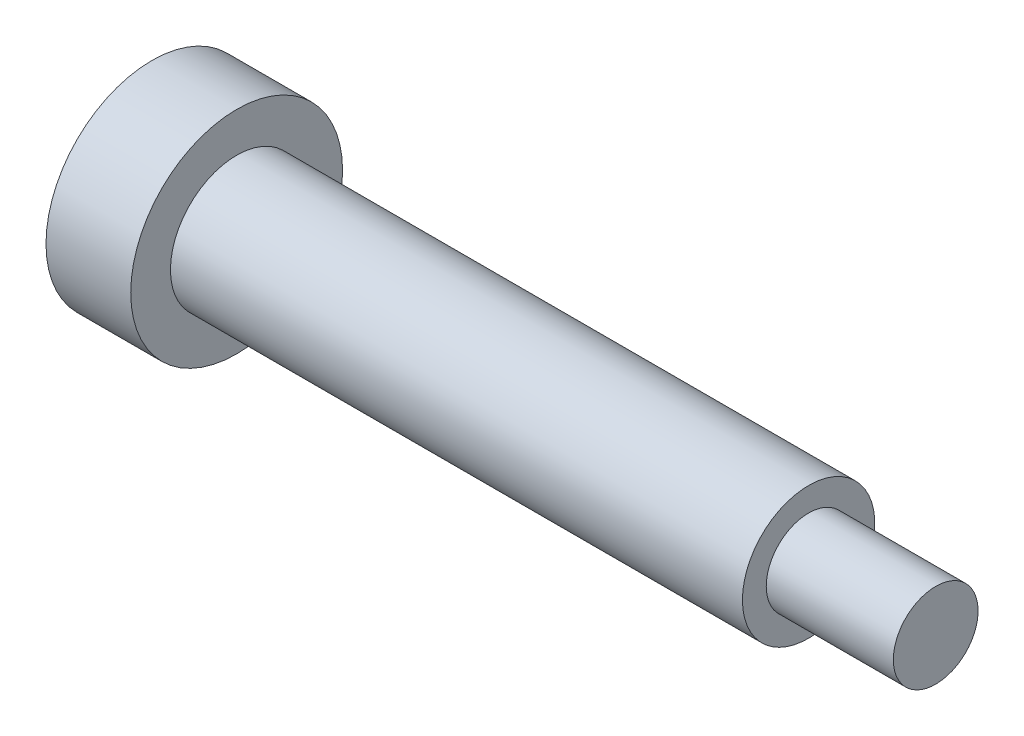
SolidWorks part; units mm, degrees
ref_plane "Front Plane" through (0, 0, 0) normal (0, 0, 1) x (1, 0, 0)
ref_plane "Top Plane" through (0, 0, 0) normal (0, 1, 0) x (1, 0, 0)
ref_plane "Right Plane" through (0, 0, 0) normal (1, 0, 0) x (0, 0, -1)
sketch "Sketch1" plane through (0, 0, 0) normal (0, 0, 1) x (1, 0, 0)
  line L0 (0, 0) -> (47.0857, 0) construction
  line L1 (0, 0) -> (0, 5)
  line L2 (0, 5) -> (4, 5)
  line L3 (4, 5) -> (4, 3.125)
  line L4 (4, 3.125) -> (31, 3.125)
  line L5 (31, 3.125) -> (31, 2)
  line L6 (31, 2) -> (37, 2)
  line L7 (37, 2) -> (37, 0)
  line L8 (0, 0) -> (37, 0)
  point P9 (47.0857, 0)
  dimension "D1" = 5
  dimension "D2" = 3.125
  dimension "D3" = 2
  dimension "D4" = 4
  dimension "D5" = 27
  dimension "D6" = 37
revolve "Revolve1" add sketch "Sketch1" angle 360 about L0
